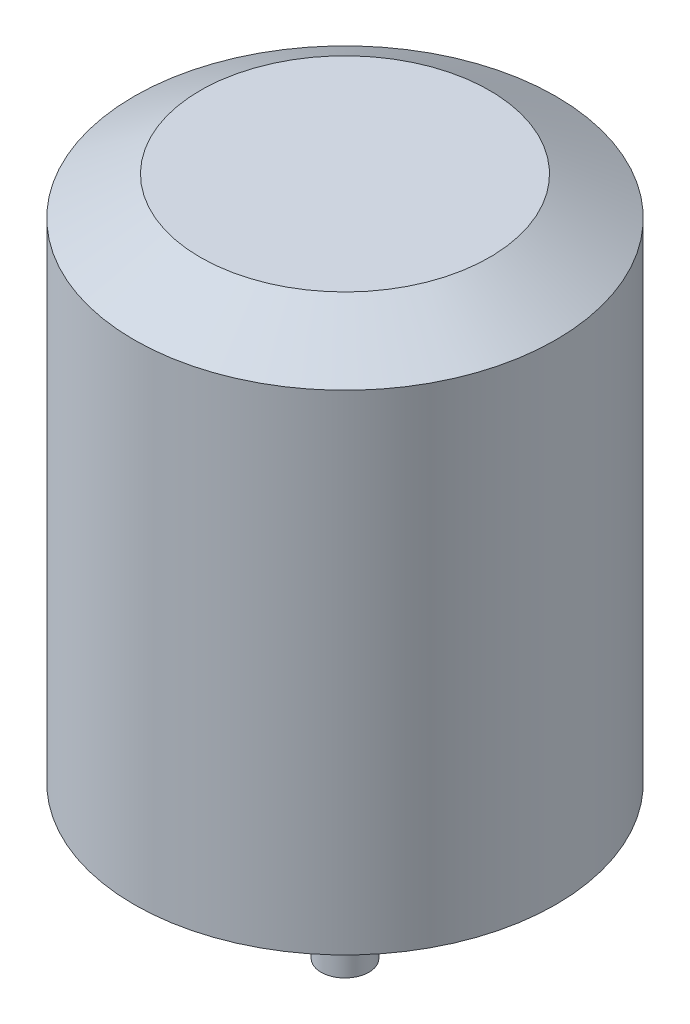
SolidWorks part; units mm, degrees
ref_plane "Front Plane" through (0, 0, 0) normal (0, 0, 1) x (1, 0, 0)
ref_plane "Top Plane" through (0, 0, 0) normal (0, 1, 0) x (1, 0, 0)
ref_plane "Right Plane" through (0, 0, 0) normal (1, 0, 0) x (0, 0, -1)
other "Bounding Box"
ref_plane "Default Plane" through (-8.9266, -12.7485, 0) normal (-0.1736, 0.9848, 0) x (0.9848, 0.1736, 0)
sketch "Sketch1" plane through (0, 0, 0) normal (0, 1, 0) x (1, 0, 0)
  circle A0 centre (0, 0) radius 14
  dimension "D1" = 28
extrude "Boss-Extrude1" add sketch "Sketch1" along normal mid plane 35
chamfer "Chamfer1" distance 2.54 angle 60 1 edges at (0, 17.5, 14)
sketch "Sketch2" plane through (0, -17.5, 0) normal (0, -1, 0) x (1, 0, 0)
  circle A0 centre (0, 0) radius 1.5875
  dimension "D1" = 3.175
extrude "Boss-Extrude2" add sketch "Sketch2" along normal offset from surface (10.1 mm away) 45.1 up to face at (0, 17.5, 9.6006)
